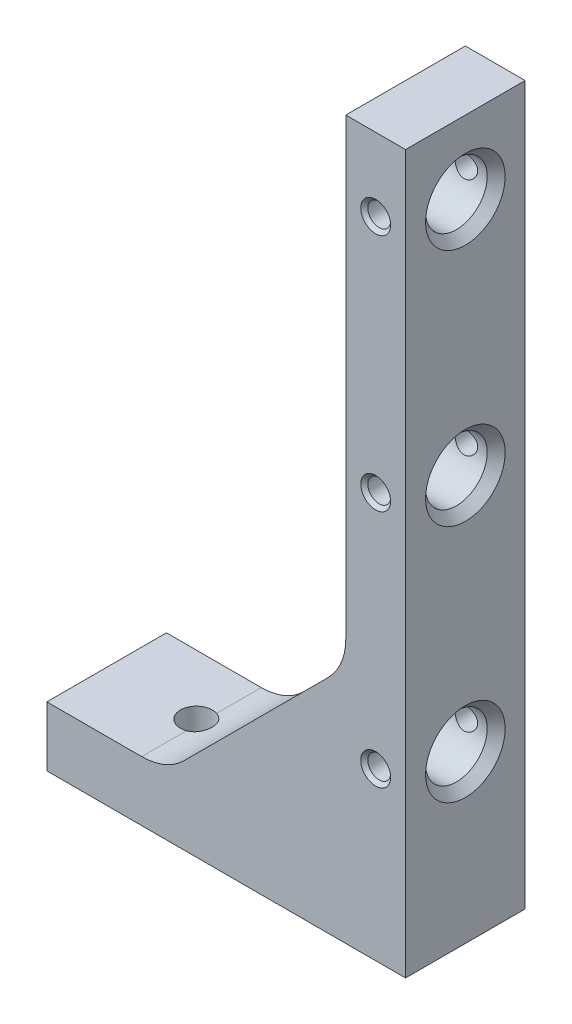
SolidWorks part; units mm, degrees
material "6061-T6 Al"
ref_plane "Front" through (0, 0, 0) normal (0, 0, 1) x (1, 0, 0)
ref_plane "Top" through (0, 0, 0) normal (0, 1, 0) x (1, 0, 0)
ref_plane "Right" through (0, 0, 0) normal (1, 0, 0) x (0, 0, -1)
sketch "Sketch1" plane through (0, 0, 0) normal (0, 0, 1) x (1, 0, 0)
  line L0 (0, 0) -> (0, 12.7)
  line L1 (0, 0) -> (76.2, 0)
  line L2 (0, 12.7) -> (20.1395, 12.7)
  line L3 (29.1197, 16.4197) -> (59.7803, 47.0803)
  line L4 (63.5, 152.4) -> (76.2, 152.4)
  line L6 (25.4, 12.7) -> (42.7636, 12.7) construction
  line L8 (76.2, 0) -> (76.2, 152.4)
  line L9 (63.5, 152.4) -> (63.5, 56.0605)
  arc A2 (63.5, 56.0605) -> (59.7803, 47.0803) centre (50.8, 56.0605) cw
  arc A3 (20.1395, 12.7) -> (29.1197, 16.4197) centre (20.1395, 25.4) ccw
  point P15 (76.2, 25.4)
  dimension "D4" = 12.7
  dimension "D1" = 76.2
  dimension "D2" = 12.7
  dimension "D3" = 45
  dimension "D5" = 25.4
  dimension "D6" = 12.7
  dimension "D7" = 152.4
extrude "Boss-Extrude1" add sketch "Sketch1" along normal blind 25.4
hole_wizard "Tapped Hole for 1/4-20 Helicoil1" positions "Sketch4" profile "Sketch3" tap size "1/4-20" standard "Helicoil® Inch"
sketch "Sketch4" plane through (0, 0, 0) normal (0, -1, 0) x (1, 0, 0)
  line L2 (19.05, 12.7) -> (50.8, 12.7) construction
  line L3 (0, 25.4) -> (0, 0) construction
  line L4 (0, 12.7) -> (19.05, 12.7) construction
  point P0 (19.05, 12.7)
  point P1 (50.8, 12.7)
  dimension "D1" = 19.05
  dimension "D2" = 31.75
sketch "Sketch3" plane through (19.05, 0, 12.7) normal (1, 0, 0) x (0, 0, -1)
  line L0 (0, 0) -> (0, 22.553)
  line L1 (0, 22.553) -> (3.3782, 20.5232)
  line L2 (3.3782, 20.5232) -> (3.3782, 0)
  line L5 (3.3782, 0) -> (0, 0)
  line L10 (0, 22.553) -> (-3.3782, 20.5232) construction
  line L11 (0, -6.35) -> (0, 107.95) construction
  dimension "Tap Drill Dia." = 6.7564
  dimension "Tap Drill Depth" = 20.5232
  dimension "Drill Angle" = 118
cosmetic thread "Hole Thread1" parameters "D1"=11.6586, "D2"=8.095
cosmetic thread "Hole Thread2" parameters "D1"=11.6586, "D2"=8.095
hole_wizard "33/64 (0.51563) Diameter Hole1" positions "Sketch6" profile "Sketch5" hole size "33/64" standard "Ansi Inch" end condition through all
sketch "Sketch6" plane through (0, 0, 0) normal (1, 0, 0) x (0, 0, -1)
  line L2 (-12.7, 0) -> (-12.7, 86.106) construction
  line L3 (-25.4, 0) -> (0, 0) construction
  line L4 (-12.7, 136.906) -> (-12.7, 86.106) construction
  point P0 (-12.7, 86.106)
  point P15 (-12.7, 136.906)
  point P20 (-12.7, 35.306)
  dimension "D1" = 86.106
  dimension "D2" = 50.8
  dimension "D3" = 50.8
sketch "Sketch5" plane through (0, 86.106, 12.7) normal (0, 1, 0) x (0, 0, 1)
  line L0 (0, 0) -> (0, 76.2)
  line L1 (0, 76.2) -> (8.4535, 76.2)
  line L2 (6.5485, 74.295) -> (6.5485, 0)
  line L5 (6.5485, 0) -> (0, 0)
  line L7 (8.4535, 76.2) -> (6.5485, 74.295)
  line L8 (-8.4535, 76.2) -> (-6.5485, 74.295) construction
  line L11 (0, -6.35) -> (0, 107.95) construction
  dimension "Thru Hole Dia." = 13.097
  dimension "Thru Hole Depth" = 76.2
  dimension "Far C'Sink Dia." = 16.907
  dimension "Far C'Sink Angle" = 90
hole_wizard "#11 (0.191) Diameter Hole1" positions "Sketch8" profile "Sketch7" hole size "#11" standard "Ansi Inch" end condition through all
sketch "Sketch8" plane through (0, 0, 25.4) normal (0, 0, 1) x (1, 0, 0)
  line L0 (69.85, 152.4) -> (69.85, 86.106) construction
  line L1 (76.2, 152.4) -> (63.5, 152.4) construction
  line L2 (0, 0) -> (76.2, 0) construction
  line L3 (69.85, 86.106) -> (69.85, 35.306) construction
  point P0 (69.85, 86.106)
  point P9 (69.85, 136.906)
  point P11 (69.85, 35.306)
  dimension "D1" = 86.106
  dimension "D2" = 50.8
  dimension "D3" = 50.8
sketch "Sketch7" plane through (69.85, 86.106, 25.4) normal (1, 0, 0) x (0, -1, 0)
  line L0 (0, 0) -> (0, 25.4)
  line L1 (0, 25.4) -> (3.175, 25.4)
  line L2 (2.4257, 24.6507) -> (2.4257, 0.7493)
  line L3 (2.4257, 0.7493) -> (3.175, 0)
  line L5 (3.175, 0) -> (0, 0)
  line L6 (-2.4257, 0.7493) -> (-3.175, 0) construction
  line L7 (3.175, 25.4) -> (2.4257, 24.6507)
  line L8 (-3.175, 25.4) -> (-2.4257, 24.6507) construction
  line L11 (0, -6.35) -> (0, 107.95) construction
  dimension "Thru Hole Dia." = 4.8514
  dimension "Thru Hole Depth" = 25.4
  dimension "Near C'Sink Dia." = 6.35
  dimension "Near C'Sink Angle" = 90
  dimension "Far C'Sink Dia." = 6.35
  dimension "Far C'Sink Angle" = 90
